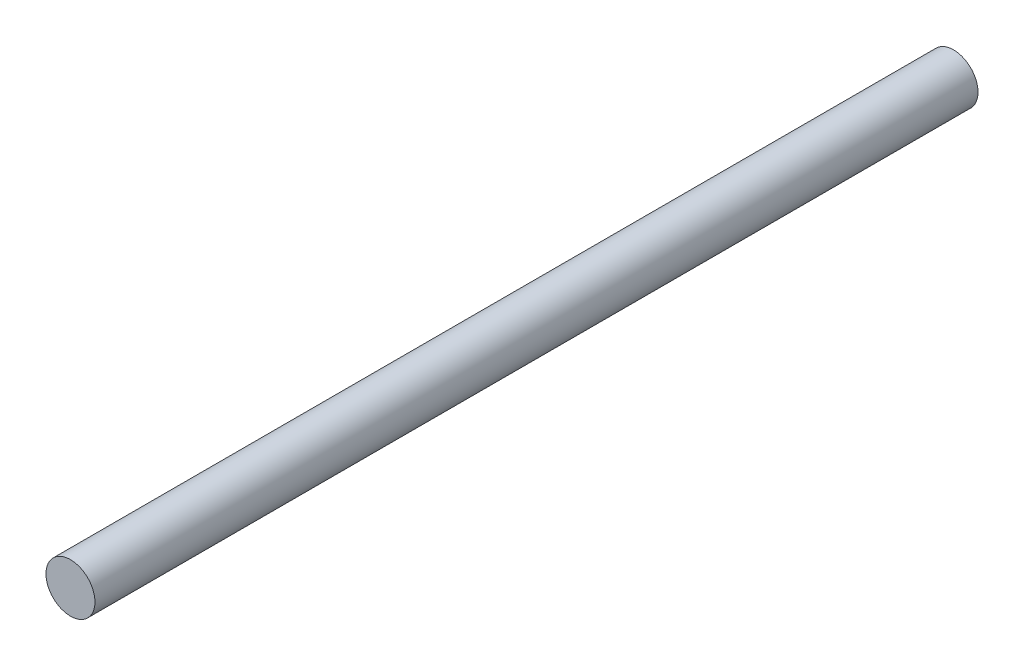
SolidWorks part; units mm, degrees
ref_plane "Front Plane" through (0, 0, 0) normal (0, 0, 1) x (1, 0, 0)
ref_plane "Top Plane" through (0, 0, 0) normal (0, 1, 0) x (1, 0, 0)
ref_plane "Right Plane" through (0, 0, 0) normal (1, 0, 0) x (0, 0, -1)
sketch "Sketch1" plane through (0, 0, 0) normal (0, 0, 1) x (1, 0, 0)
  circle A0 centre (11.574, 0.2081) radius 2.0801
extrude "Boss-Extrude1" add sketch "Sketch1" against normal blind 75
